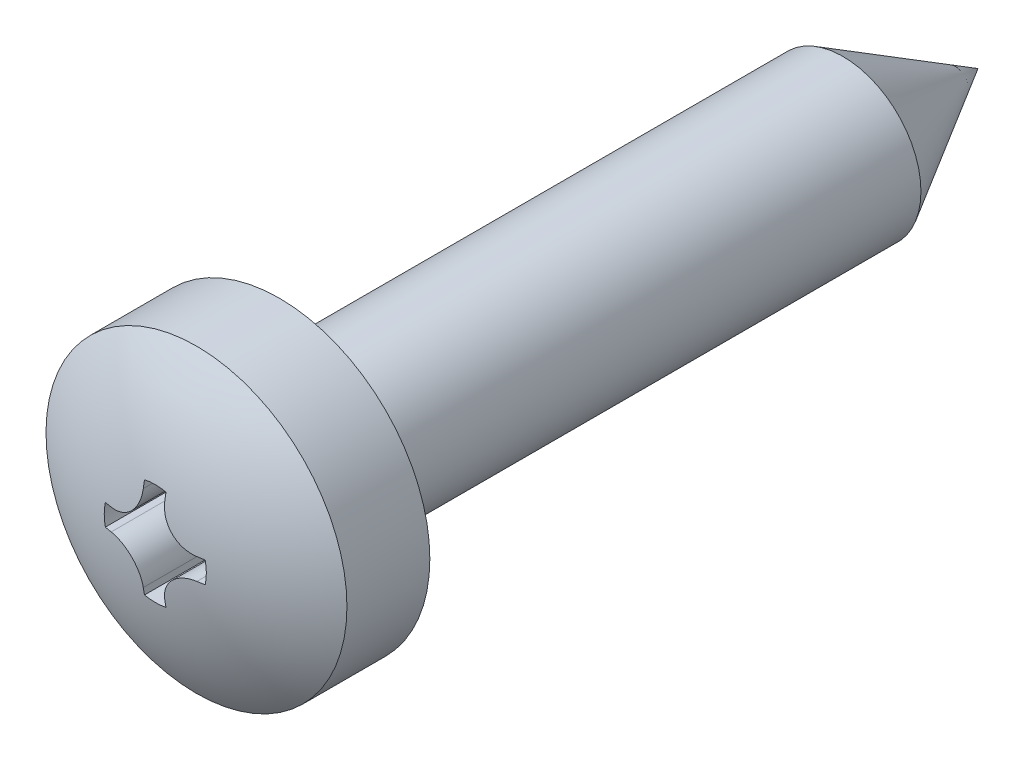
SolidWorks part; units mm, degrees
revolve "基体-旋转" add sketch "草图8" angle 360 about L0
sketch "草图8" plane through (0, 0, 0) normal (1, 0, 0) x (0, 0, -1)
  line L0 (-11.71, 0) -> (1.33, 0) construction
  line L1 (0, 0) -> (-15.4, 0)
  line L4 (-14.5425, 2.8) -> (-13, 2.8)
  line L5 (-13, 2.8) -> (-13, 1.45)
  line L6 (-13, 1.45) -> (-2.5115, 1.45)
  line L7 (-2.5115, 1.45) -> (0, 0)
  arc A0 (-15.4, 0) -> (-14.5425, 2.8) centre (-10.4, 0) cw
  dimension "D4" = 5
  dimension "D1" = 13
  dimension "D2" = 30
  dimension "D5" = 2.9
  dimension "D3" = 5.6
  dimension "D6" = 2.4
cosmetic thread "装饰螺纹线1" parameters "D1"=9.3, "D2"=2.5114
extrude "切除-拉伸2" cut sketch "草图7" against normal blind 1.2
sketch "草图7" plane through (0, 0, 15.4) normal (0, 0, 1) x (1, 0, 0)
  line L0 (-7.1, 0) -> (5.9, 0) construction
  line L1 (0, 7.5) -> (0, -7) construction
  line L2 (0.2, 0.9287) -> (0.2, 0.7975)
  line L3 (0, 0) -> (4.9858, 4.9858) construction
  line L4 (0.9287, 0.2) -> (0.7975, 0.2)
  line L5 (0.9287, -0.2) -> (0.7975, -0.2)
  line L6 (0.2, -0.9287) -> (0.2, -0.7975)
  line L7 (-0.2, -0.9287) -> (-0.2, -0.7975)
  line L8 (-0.9287, -0.2) -> (-0.7975, -0.2)
  line L9 (-0.9287, 0.2) -> (-0.7975, 0.2)
  line L10 (-0.2, 0.9287) -> (-0.2, 0.7975)
  line L11 (0, 0) -> (-4.9858, 4.9858) construction
  arc A0 (-0.2, 0.9287) -> (0.2, 0.9287) centre (0, 0) cw
  arc A1 (0.9287, -0.2) -> (0.9287, 0.2) centre (0, 0) ccw
  arc A2 (0.7975, 0.2) -> (0.2, 0.7975) centre (0.7975, 0.7975) cw
  arc A3 (-0.7975, 0.2) -> (-0.2, 0.7975) centre (-0.7975, 0.7975) ccw
  arc A4 (-0.2, -0.9287) -> (0.2, -0.9287) centre (0, 0) ccw
  arc A5 (0.7975, -0.2) -> (0.2, -0.7975) centre (0.7975, -0.7975) ccw
  arc A6 (-0.9287, -0.2) -> (-0.9287, 0.2) centre (0, 0) cw
  arc A7 (-0.7975, -0.2) -> (-0.2, -0.7975) centre (-0.7975, -0.7975) cw
  dimension "D10" = 0.95
  dimension "D1" = 0.5975
  dimension "D2" = 0.5975
material "冷镦钢"
ref_plane "前视" through (0, 0, 0) normal (0, 0, 1) x (1, 0, 0)
ref_plane "上视" through (0, 0, 0) normal (0, 1, 0) x (1, 0, 0)
ref_plane "右视" through (0, 0, 0) normal (1, 0, 0) x (0, 0, -1)
sketch "尺寸草图" plane through (0, 0, 0) normal (1, 0, 0) x (0, 0, -1)
  line L0 (-13, 5.6) -> (-13, 0)
  line L1 (-13, 0) -> (0, 0)
  line L2 (0, 0) -> (0, 2.9)
  point P4 (-10.6, 0)
  point P6 (0, 1.1)
  point P7 (-11.9, 0)
  point P8 (-13, 5.5)
  point P9 (-13, 0.6)
  point P10 (-1.9, 0)
  point P11 (-1.2, 0)
  point P12 (-12.52, 0)
  point P13 (-9.5, 0)
  point P14 (-10.4, 0)
  dimension "l" = 13
  dimension "E" = 5.6
  dimension "K" = 2.4
  dimension "d" = 2.9
  dimension "P" = 1.1
  dimension "A" = 1.1
  dimension "R" = 0.1
  dimension "Rf" = 5
  dimension "HM" = 1.9
  dimension "HH" = 1.2
  dimension "HE" = 0.48
  dimension "Da" = 3.5
  dimension "Yc" = 2.6
ref_plane "基准面6" through (0, 0, 15.4) normal (0, 0, 1) x (1, 0, 0)
sketch "草图9" plane through (0, 0, 0) normal (1, 0, 0) x (0, 0, -1)
  line L0 (-11.9, 1.45) -> (-10.8, 1.45)
  line L1 (-11.9, 1.45) -> (-11.4875, 0.9)
  line L2 (-11.2125, 0.9) -> (-11.4875, 0.9)
  line L3 (-11.2125, 0.9) -> (-10.8, 1.45)
  line L4 (-11.71, 0) -> (1.33, 0) construction
  line L5 (-13, -2.8) -> (-13, 2.8) construction
  line L6 (-6.912, 0) -> (-2.6011, 0) construction
  line L7 (-14.2, 0) -> (-15.3089, 0) construction
  dimension "D1" = 1.1
  dimension "D2" = 0.275
  dimension "D3" = 0.55
  dimension "D4" = 1.45
  dimension "D5" = 1.1
revolve "切除-旋转1" [suppressed] cut sketch "草图9" angle 360 about L6
pattern_linear "阵列(线性)1" [suppressed] count 9 spacing 1.375
fillet "圆角1" radius 0.1 1 edges at (1.45, 0, 13)
equation "\"D16@基准面6\" = \"l@尺寸草图\"+\"K@尺寸草图\""
equation "\"D1@草图8\" = \"l@尺寸草图\""
equation "\"D6@草图8\" = \"K@尺寸草图\""
equation "\"D5@草图8\" = \"d@尺寸草图\""
equation "\"D3@草图8\" = \"E@尺寸草图\""
equation "\"D4@草图8\" = \"Rf@尺寸草图\""
equation "\"D10@草图7\" = \"HM@尺寸草图\"/2"
equation "\"D1@切除-拉伸2\" = \"HH@尺寸草图\""
equation "\"D1@草图9\" = \"P@尺寸草图\""
equation "\"D2@草图9\" = \"D1@草图9\"/4"
equation "\"D3@草图9\" = \"D1@草图9\"/2"
equation "\"D4@草图9\" = \"d@尺寸草图\"/2"
equation "\"D5@草图9\" = \"A@尺寸草图\""
equation "\"D3@阵列(线性)1\" = \"A@尺寸草图\"*5/4"
equation "\"D1@阵列(线性)1\" = (\"l@尺寸草图\"-\"A@尺寸草图\")/\"D3@阵列(线性)1\""
equation "\"D2@装饰螺纹线1\" = \"d@尺寸草图\"*0.866"
equation "\"D1@装饰螺纹线1\" = \"l@尺寸草图\"-\"Yc@尺寸草图\"-\"A@尺寸草图\""
equation "\"D1@圆角1\" = \"R@尺寸草图\""
